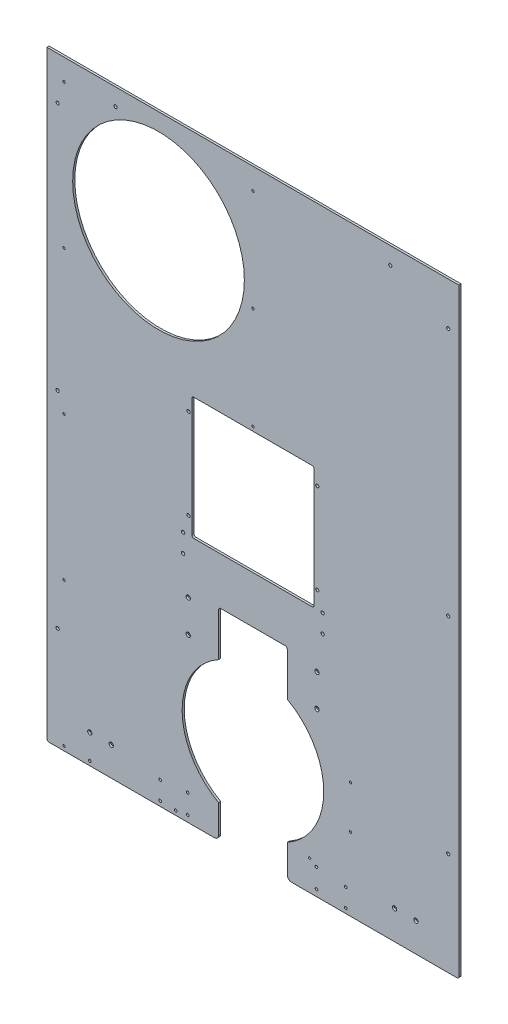
SolidWorks part; units mm, degrees
material "PC High Viscosity"
ref_plane "Front Plane" through (0, 0, 0) normal (0, 0, 1) x (1, 0, 0)
ref_plane "Top Plane" through (0, 0, 0) normal (0, 1, 0) x (1, 0, 0)
ref_plane "Right Plane" through (0, 0, 0) normal (1, 0, 0) x (0, 0, -1)
sketch "Sketch1" plane through (0, 0, 0) normal (0, 0, 1) x (1, 0, 0)
  line L2 (0, 0) -> (0, 1778)
  line L3 (0, 1778) -> (1219.2, 1778)
  line L4 (1219.2, 0) -> (1219.2, 1778)
  line L5 (428.625, 736.6) -> (790.575, 736.6)
  line L6 (428.625, 736.6) -> (428.625, 1098.55)
  line L7 (428.625, 1098.55) -> (790.575, 1098.55)
  line L8 (790.575, 736.6) -> (790.575, 1098.55)
  line L15 (0, 0) -> (1219.2, 0)
  circle A1 centre (330.2, 1473.2) radius 254
  point P7 (609.6, 1098.55)
  dimension "D3" = 736.6
  dimension "D6" = 508
  dimension "D7" = 330.2
  dimension "D1" = 1219.2
  dimension "D2" = 1778
  dimension "D4" = 361.95
  dimension "D5" = 609.6
  dimension "D8" = 1473.2
extrude "Boss-Extrude1" add sketch "Sketch1" along normal blind 6.35
sketch "Sketch3" plane through (0, 0, 6.35) normal (0, 0, 1) x (1, 0, 0)
  line L0 (0, 0) -> (1219.2, 0) construction
  line L2 (428.625, 736.6) -> (790.575, 736.6) construction
  circle A0 centre (609.6, 279.4) radius 209.55
  point P5 (609.6, 736.6)
  dimension "D1" = 419.1
  dimension "D2" = 279.4
extrude "Cut-Extrude2" cut sketch "Sketch3" against normal through all
sketch "Sketch2" plane through (0, 0, 6.35) normal (0, 0, 1) x (1, 0, 0)
  line L1 (508, 127) -> (711.2, 127)
  line L2 (508, 127) -> (508, -38.1)
  line L3 (508, -38.1) -> (711.2, -38.1)
  line L4 (711.2, 127) -> (711.2, -38.1)
  line L6 (508, 596.9) -> (711.2, 596.9)
  line L7 (508, 596.9) -> (508, 431.8)
  line L8 (508, 431.8) -> (711.2, 431.8)
  line L9 (711.2, 596.9) -> (711.2, 431.8)
  line L10 (790.575, 1098.55) -> (428.625, 1098.55) construction
  circle A0 centre (609.6, 279.4) radius 241.3 construction
  point P12 (609.6, 596.9)
  point P15 (609.6, 1098.55)
  point P16 (609.6, -38.1)
  point P17 (609.6, 431.8)
  dimension "D3" = 482.6
  dimension "D4" = 165.1
  dimension "D2" = 317.5
  dimension "D5" = 317.5
  dimension "D1" = 203.2
  dimension "D6" = 165.1
extrude "Cut-Extrude1" cut sketch "Sketch2" against normal through all
sketch "Sketch4" plane through (0, 0, 6.35) normal (0, 0, 1) x (1, 0, 0)
  line L1 (0, 0) -> (508, 0) construction
  line L6 (0, 1778) -> (0, 0) construction
  circle A0 centre (50.8, 12.7) radius 3.3655
  dimension "D1" = 6.731
  dimension "D2" = 12.7
  dimension "D3" = 50.8
extrude "Cut-Extrude3" cut sketch "Sketch4" against normal through all
pattern_linear "LPattern1" count 5 spacing 425.45 along (0, 1, 0) of "Cut-Extrude3"
sketch "Sketch5" plane through (0, 0, 6.35) normal (0, 0, 1) x (1, 0, 0)
  line L0 (1219.2, 1778) -> (0, 1778) construction
  line L1 (0, 1778) -> (0, 0) construction
  circle A0 centre (609.6, 1714.5) radius 3.429
  dimension "D1" = 63.5
  dimension "D2" = 6.858
  dimension "D3" = 609.6
extrude "Cut-Extrude4" cut sketch "Sketch5" against normal through all
pattern_linear "LPattern2" count 3 spacing 301.625 along (0, -1, 0) of "Cut-Extrude4"
sketch "Sketch6" plane through (0, 0, 6.35) normal (0, 0, 1) x (1, 0, 0)
  line L0 (0, 0) -> (508, 0) construction
  line L2 (0, 1778) -> (0, 0) construction
  circle A0 centre (127, 12.7) radius 3.9687
  circle A1 centre (381, 12.7) radius 3.9688
  dimension "D1" = 12.7
  dimension "D3" = 7.9375
  dimension "D2" = 254
  dimension "D4" = 127
extrude "Cut-Extrude5" cut sketch "Sketch6" against normal through all
sketch "Sketch7" plane through (0, 0, 6.35) normal (0, 0, 1) x (1, 0, 0)
  line L1 (711.2, 0) -> (1219.2, 0) construction
  circle A0 centre (777.6052, 88.9) radius 3.3782
  circle A1 centre (609.6, 279.4) radius 241.3 construction
  circle A2 centre (777.6052, 88.9) radius 12.7 construction
  circle A3 centre (609.6, 279.4) radius 254 construction
  circle A4 centre (898.525, 342.9) radius 3.3782
  circle A5 centre (898.525, 215.9) radius 3.3782
  dimension "D1" = 63.5
  dimension "D3" = 6.7564
  dimension "D4" = 482.6
  dimension "D5" = 25.4
  dimension "D6" = 508
  dimension "D2" = 88.9
  dimension "D7" = 127
  dimension "D12" = 288.925
  dimension "D13" = 215.9
extrude "Cut-Extrude6" cut sketch "Sketch7" against normal through all contours A4 | A5 | A0
sketch "Sketch9" plane through (0, 0, 6.35) normal (0, 0, 1) x (1, 0, 0)
  line L0 (0, 0) -> (508, 0) construction
  line L1 (0, 1778) -> (0, 0) construction
  point P0 (127, 85.725)
  point P1 (190.5, 85.725)
  dimension "D1" = 63.5
  dimension "D2" = 85.725
  dimension "D3" = 127
hole_wizard "CSK for 1/4 Flat Head Machine Screw1" positions "Sketch10" profile "Sketch11" countersink size "1/4" standard "ANSI Inch" end condition through all
sketch "Sketch10" plane through (0, 0, 6.35) normal (0, 0, 1) x (1, 0, 0)
  point P0 (127, 85.725)
  point P3 (190.5, 85.725)
sketch "Sketch11" plane through (127, 85.725, 6.35) normal (1, 0, 0) x (0, -1, 0)
  line L0 (0, 0) -> (0, 6.35)
  line L1 (0, 6.35) -> (3.5712, 6.35)
  line L2 (3.5712, 6.35) -> (3.5712, 3.2989)
  line L3 (3.5712, 3.2989) -> (6.4389, 0)
  line L5 (6.4389, 0) -> (0, 0)
  line L6 (-3.5712, 3.2989) -> (-6.4389, 0) construction
  line L11 (0, -6.35) -> (0, 107.95) construction
  dimension "Thru Hole Dia." = 7.1425
  dimension "Thru Hole Depth" = 6.35
  dimension "Near C'Sink Dia." = 12.8778
  dimension "Near C'Sink Angle" = 82
pattern_linear "LPattern3" count 2 spacing 901.7 along (1, 0, 0) of "CSK for 1/4 Flat Head Machine Screw1"
sketch "Sketch12" plane through (0, 0, 6.35) normal (0, 0, 1) x (1, 0, 0)
  line L0 (0, 1778) -> (0, 0) construction
  line L1 (1219.2, 0) -> (1219.2, 1778) construction
  line L2 (1219.2, 1778) -> (0, 1778) construction
  circle A0 centre (203.2, 1727.2) radius 4.7625
  circle A1 centre (1016, 1727.2) radius 4.7625
  dimension "D1" = 203.2
  dimension "D4" = 9.525
  dimension "D2" = 203.2
  dimension "D3" = 50.8
extrude "Cut-Extrude7" cut sketch "Sketch12" against normal through all
ref_plane "Plane1" through (609.6, 0, 0) normal (-1, 0, 0) x (0, 0, 1)
sketch "Sketch14" plane through (0, 0, 6.35) normal (0, 0, 1) x (1, 0, 0)
  line L0 (0, 1778) -> (0, 0) construction
  line L1 (1219.2, 1778) -> (0, 1778) construction
  line L2 (0, 0) -> (508, 0) construction
  circle A0 centre (31.75, 1651) radius 4.7625
  circle A1 centre (31.75, 914.4) radius 4.7625
  circle A2 centre (31.75, 304.8) radius 4.7625
  dimension "D1" = 31.75
  dimension "D2" = 9.525
  dimension "D3" = 127
  dimension "D4" = 304.8
  dimension "D5" = 914.4
extrude "Cut-Extrude8" cut sketch "Sketch14" against normal through all
mirror "Mirror1" about plane through (609.6, 0, 0) normal (-1, 0, 0) of "Cut-Extrude8"
sketch "Sketch15" plane through (0, 0, 6.35) normal (0, 0, 1) x (1, 0, 0)
  line L0 (428.625, 736.6) -> (790.575, 736.6) construction
  line L1 (428.625, 1098.55) -> (428.625, 736.6) construction
  circle A0 centre (403.225, 736.6) radius 4.7625
  circle A1 centre (403.225, 682.625) radius 4.7625
  dimension "D1" = 53.975
  dimension "D3" = 9.525
  dimension "D2" = 25.4
extrude "Cut-Extrude9" cut sketch "Sketch15" against normal through all
mirror "Mirror2" about plane through (609.6, 0, 0) normal (-1, 0, 0) of "Cut-Extrude9"
sketch "Sketch16" plane through (0, 0, 6.35) normal (0, 0, 1) x (1, 0, 0)
  line L0 (428.625, 1098.55) -> (428.625, 736.6) construction
  line L1 (428.625, 736.6) -> (790.575, 736.6) construction
  line L2 (790.575, 736.6) -> (790.575, 1098.55) construction
  circle A0 centre (419.1, 1054.1) radius 4.7625
  circle A1 centre (419.1, 787.4) radius 4.7625
  circle A2 centre (800.1, 1054.1) radius 4.7625
  circle A3 centre (800.1, 787.4) radius 4.7625
  dimension "D1" = 9.525
  dimension "D2" = 9.525
  dimension "D3" = 266.7
  dimension "D4" = 50.8
  dimension "D5" = 9.525
extrude "Cut-Extrude10" cut sketch "Sketch16" against normal through all
fillet "Fillet1" radius 12.7 2 edges at (711.2, 0, 3.175) (508, 0, 3.175)
fillet "Fillet2" radius 6.35 8 edges at (508, 596.9, 3.175) (711.2, 596.9, 3.175) (790.575, 736.6, 3.175) (790.575, 1098.55, 3.175) (428.625, 1098.55, 3.175) (428.625, 736.6, 3.175) (0, 0, 3.175) (1219.2, 0, 3.175)
sketch "Sketch17" plane through (0, 0, 6.35) normal (0, 0, 1) x (1, 0, 0)
  line L0 (44.45, 0) -> (463.55, 0) construction
  line L1 (0, 1778) -> (0, 6.35) construction
  circle A4 centre (416.5676, 76.2) radius 3.937
  circle A5 centre (416.5676, 19.05) radius 3.937
  circle A6 centre (797.5676, 19.05) radius 3.937
  circle A7 centre (797.5676, 76.2) radius 3.937
  dimension "D3" = 381
  dimension "D4" = 19.05
  dimension "D1" = 7.874
  dimension "D2" = 57.15
  dimension "D5" = 416.5676
extrude "Cut-Extrude11" cut sketch "Sketch17" against normal through all
sketch "Sketch18" plane through (0, 0, 6.35) normal (0, 0, 1) x (1, 0, 0)
  line L0 (0, 1778) -> (0, 6.35) construction
  line L1 (723.9, 0) -> (1212.85, 0) construction
  circle A0 centre (418.1551, 576.972) radius 3.9687
  circle A1 centre (418.1551, 481.722) radius 3.9687
  circle A2 centre (799.1551, 481.722) radius 3.9687
  circle A3 centre (799.1551, 576.972) radius 3.9687
  dimension "D2" = 7.9375
  dimension "D1" = 95.25
  dimension "D3" = 381
  dimension "D4" = 418.1551
  dimension "D5" = 481.722
hole_wizard "CSK for 1/4 Flat Head Machine Screw2" positions "Sketch20" profile "Sketch21" countersink size "1/4" standard "ANSI Inch" end condition up to next
sketch "Sketch20" plane through (0, 0, 6.35) normal (0, 0, 1) x (1, 0, 0)
  point P0 (418.1551, 576.972)
  point P3 (418.1551, 481.722)
  point P6 (799.1551, 576.972)
  point P9 (799.1551, 481.722)
sketch "Sketch21" plane through (418.1551, 576.972, 6.35) normal (1, 0, 0) x (0, -1, 0)
  line L0 (0, 0) -> (0, 6.35)
  line L1 (0, 6.35) -> (3.5712, 6.35)
  line L2 (3.5712, 6.35) -> (3.5712, 3.2989)
  line L3 (3.5712, 3.2989) -> (6.4389, 0)
  line L5 (6.4389, 0) -> (0, 0)
  line L6 (-3.5712, 3.2989) -> (-6.4389, 0) construction
  line L11 (0, -6.35) -> (0, 107.95) construction
  dimension "Thru Hole Dia." = 7.1425
  dimension "Thru Hole Depth" = 6.35
  dimension "Near C'Sink Dia." = 12.8778
  dimension "Near C'Sink Angle" = 82
hole_wizard "5/16 (0.3125) Diameter Hole1" positions "Sketch22" profile "Sketch23" hole size "5/16" standard "ANSI Inch" end condition through all
sketch "Sketch22" plane through (0, 0, 6.35) normal (0, 0, 1) x (1, 0, 0)
  line L0 (0, 1778) -> (0, 6.35) construction
  line L1 (6.35, 0) -> (495.3, 0) construction
  line L2 (609.6, 0) -> (609.6, 1778) construction
  line L3 (1219.2, 1778) -> (0, 1778) construction
  line L5 (723.9, 0) -> (1212.85, 0) construction
  point P0 (334.9625, 68.2625)
  point P2 (334.9625, 14.2875)
  point P16 (609.6, 1778)
  point P17 (609.6, 15.0812)
  point P20 (884.2375, 14.2875)
  point P21 (884.2375, 68.2625)
  dimension "D1" = 334.9625
  dimension "D2" = 14.2875
  dimension "D3" = 53.975
sketch "Sketch23" plane through (334.9625, 68.2625, 6.35) normal (1, 0, 0) x (0, -1, 0)
  line L0 (0, 0) -> (0, 6.35)
  line L1 (0, 6.35) -> (3.9687, 6.35)
  line L2 (3.9687, 6.35) -> (3.9687, 0)
  line L5 (3.9687, 0) -> (0, 0)
  line L11 (0, -6.35) -> (0, 107.95) construction
  dimension "Thru Hole Dia." = 7.9375
  dimension "Thru Hole Depth" = 6.35
